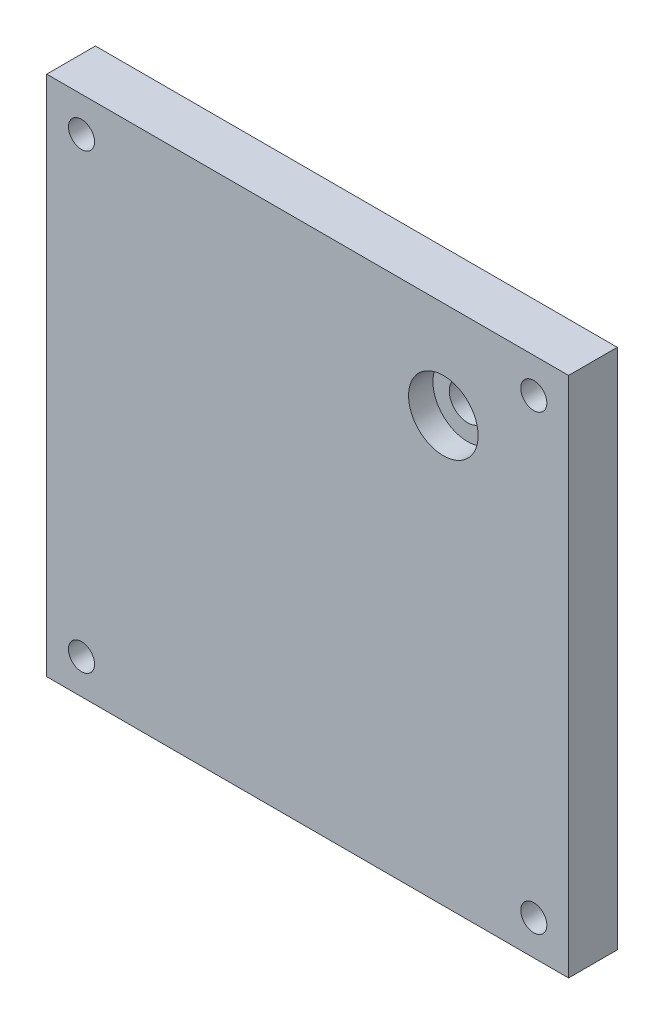
SolidWorks part; units mm, degrees
ref_plane "Front Plane" through (0, 0, 0) normal (0, 0, 1) x (1, 0, 0)
ref_plane "Top Plane" through (0, 0, 0) normal (0, 1, 0) x (1, 0, 0)
ref_plane "Right Plane" through (0, 0, 0) normal (1, 0, 0) x (0, 0, -1)
sketch "Sketch1" plane through (0, 0, 0) normal (0, 0, 1) x (1, 0, 0)
  line L1 (-47.625, -47.625) -> (47.625, -47.625)
  line L2 (-47.625, -47.625) -> (-47.625, 47.625)
  line L3 (-47.625, 47.625) -> (47.625, 47.625)
  line L4 (47.625, -47.625) -> (47.625, 47.625)
  line L5 (-47.625, -47.625) -> (47.625, 47.625) construction
  line L6 (-47.625, 47.625) -> (47.625, -47.625) construction
  point P0 (0, 0)
  dimension "D1" = 95.25
  dimension "D2" = 95.25
extrude "Boss-Extrude1" add sketch "Sketch1" along normal blind 8.89
sketch "Sketch2" plane through (0, 0, 8.89) normal (0, 0, 1) x (1, 0, 0)
  line L0 (47.625, 47.625) -> (-47.625, 47.625) construction
  line L1 (-47.625, -47.625) -> (47.625, -47.625)
  line L2 (-47.625, -47.625) -> (-47.625, 47.625)
  line L3 (-47.625, 47.625) -> (47.625, 47.625)
  line L4 (47.625, -47.625) -> (47.625, 47.625)
  line L5 (-47.625, -47.625) -> (47.625, 47.625) construction
  line L6 (-47.625, 47.625) -> (47.625, -47.625) construction
  line L7 (47.625, -47.625) -> (47.625, 47.625) construction
  line L9 (36.195, -41.275) -> (-36.195, -41.275) construction
  line L10 (41.275, -36.195) -> (41.275, 36.195) construction
  line L11 (36.195, 41.275) -> (-36.195, 41.275) construction
  line L12 (-41.275, -36.195) -> (-41.275, 36.195) construction
  line L13 (41.275, -41.275) -> (-41.275, 41.275) construction
  line L14 (41.275, 41.275) -> (-41.275, -41.275) construction
  arc A0 (-41.275, 36.195) -> (-36.195, 41.275) centre (-41.275, 41.275) ccw construction
  arc A1 (36.195, 41.275) -> (41.275, 36.195) centre (41.275, 41.275) ccw construction
  arc A2 (41.275, -36.195) -> (36.195, -41.275) centre (41.275, -41.275) ccw construction
  arc A3 (-36.195, -41.275) -> (-41.275, -36.195) centre (-41.275, -41.275) ccw construction
  circle A4 centre (-41.275, 41.275) radius 2.3812
  circle A5 centre (41.275, 41.275) radius 2.3812
  circle A6 centre (41.275, -41.275) radius 2.3812
  circle A7 centre (-41.275, -41.275) radius 2.3812
  point P0 (0, 0)
  point P10 (0, 0)
  dimension "D2" = 5.08
  dimension "D3" = 4.7625
  dimension "D1" = 6.35
extrude "Cut-Extrude2" cut sketch "Sketch2" against normal through all flip side to cut
ref_plane "Plane1" through (0, 0, 8.89) normal (0, 0, 1) x (1, 0, 0)
sketch "Sketch3" plane through (0, 0, 8.89) normal (0, 0, 1) x (1, 0, 0)
  line L0 (47.625, -47.625) -> (47.625, 47.625) construction
  line L1 (47.625, 47.625) -> (-47.625, 47.625) construction
  circle A0 centre (24.765, 29.845) radius 6.35
  dimension "D1" = 12.7
  dimension "D2" = 22.86
  dimension "D3" = 17.78
extrude "Cut-Extrude3" cut sketch "Sketch3" against normal blind 4.445 contours A0
sketch "Sketch4" plane through (0, 0, 4.445) normal (0, 0, 1) x (1, 0, 0)
  circle A0 centre (24.765, 29.845) radius 3.3655
  dimension "D1" = 6.731
extrude "Cut-Extrude4" cut sketch "Sketch4" against normal through all
